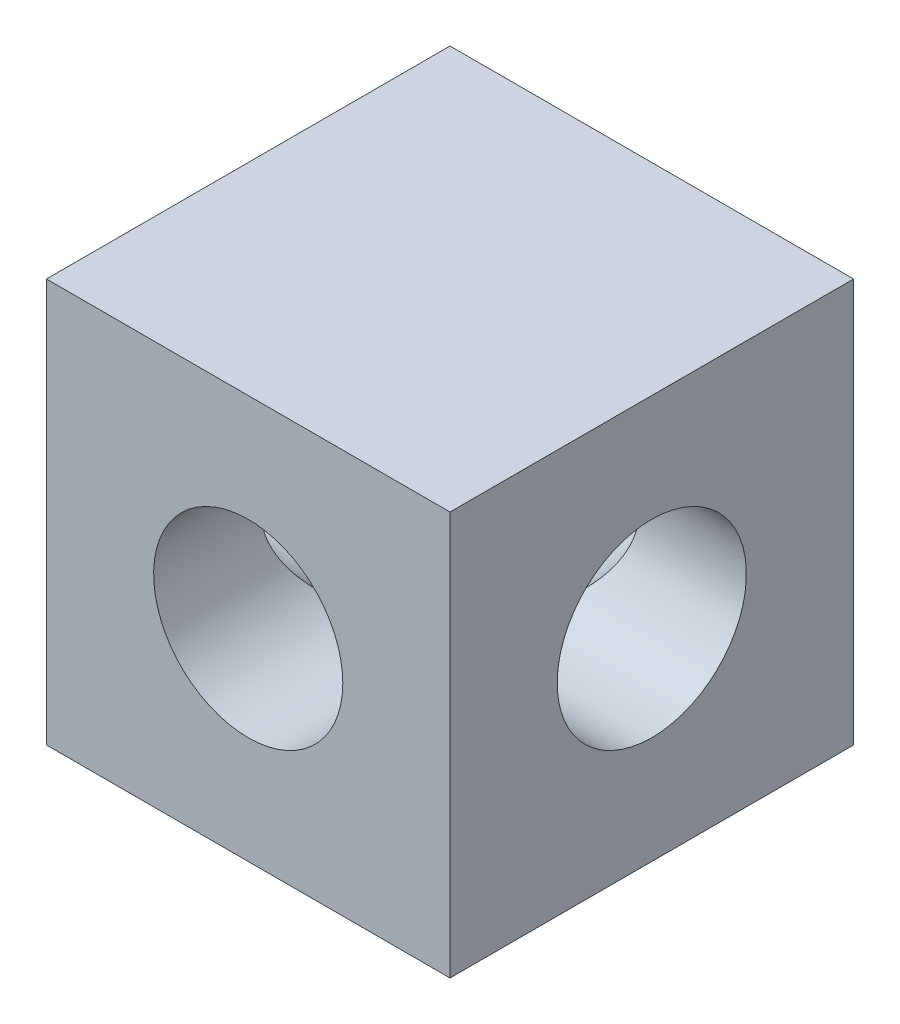
SolidWorks part; units mm, degrees
ref_plane "Front" through (0, 0, 0) normal (0, 0, 1) x (1, 0, 0)
ref_plane "Top" through (0, 0, 0) normal (0, 1, 0) x (-1, 0, 0)
ref_plane "Right" through (0, 0, 0) normal (1, 0, 0) x (0, 0, -1)
sketch "Sketch1" plane through (0, 0, 0) normal (0, 0, 1) x (1, 0, 0)
  line L0 (-27.1383, -1.6247) -> (-6.8183, -1.6247)
  line L1 (-27.1383, -1.6247) -> (-27.1383, 18.6953)
  line L2 (-6.8183, 18.6953) -> (-27.1383, 18.6953)
  line L3 (-6.8183, 18.6953) -> (-6.8183, -1.6247)
  line L4 (-6.8183, 18.6953) -> (-27.1383, -1.6247) construction
  circle A0 centre (-16.9783, 8.5353) radius 4.7625
  dimension "hole_dependent" = 9.525
  dimension "D1" = 20.32
  dimension "D2" = 20.32
extrude "Base-Extrude" add sketch "Sketch1" along normal blind 20.32
sketch "Sketch3" plane through (-6.8183, 0, 0) normal (1, 0, 0) x (0, 0, -1)
  line L0 (0, 18.6953) -> (-20.32, -1.6247) construction
  circle A0 centre (-10.16, 8.5353) radius 4.7625
  dimension "hole-independent" = 9.525
extrude "Cut-Extrude1" cut sketch "Sketch3" against normal through all
equation "\"hole_dependent@Sketch1\" = \"hole-independent@Sketch3\""
